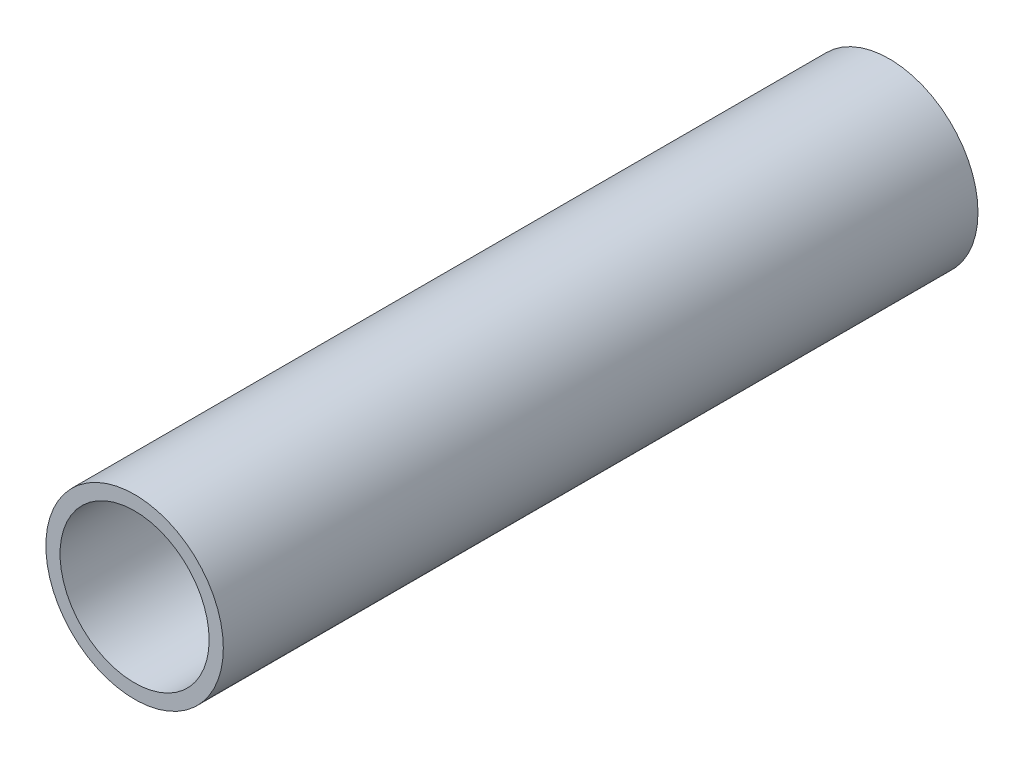
SolidWorks part; units mm, degrees
ref_plane "Front Plane" through (0, 0, 0) normal (0, 0, 1) x (1, 0, 0)
ref_plane "Top Plane" through (0, 0, 0) normal (0, 1, 0) x (1, 0, 0)
ref_plane "Right Plane" through (0, 0, 0) normal (1, 0, 0) x (0, 0, -1)
sketch "Sketch2" plane through (0, 0, 0) normal (0, 0, 1) x (1, 0, 0)
  circle A0 centre (0, 0) radius 6.35
  circle A1 centre (0, 0) radius 5.334
  dimension "D1" = 12.7
  dimension "D2" = 1.016
extrude "Boss-Extrude1" add sketch "Sketch2" along normal blind 54
